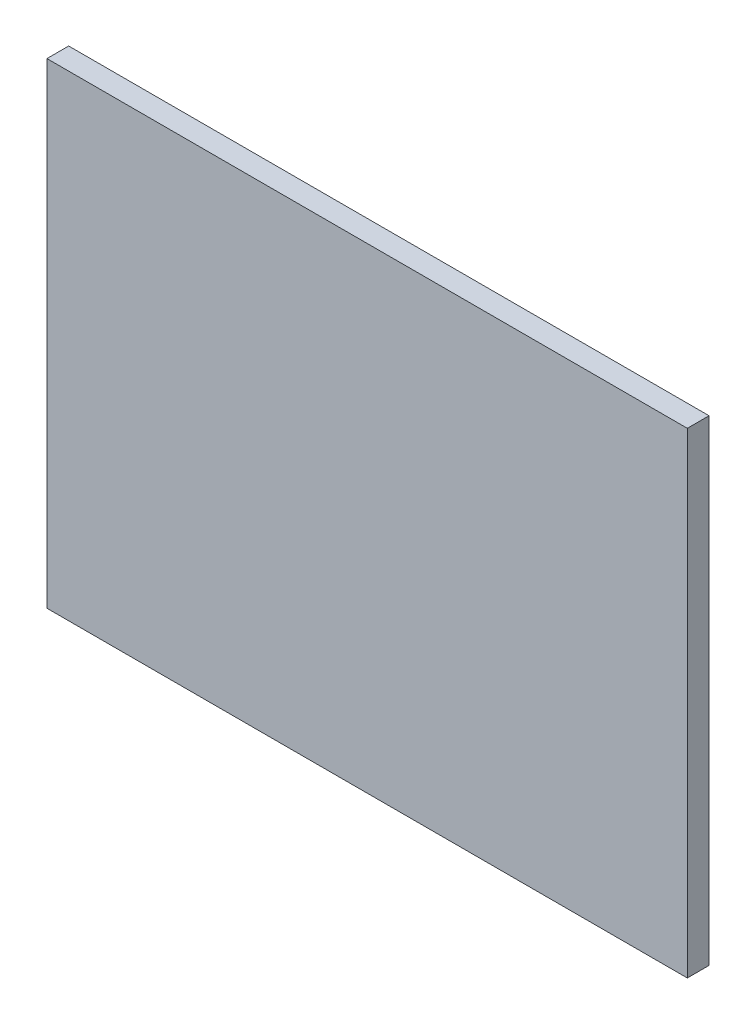
SolidWorks part; units mm, degrees
material "Balsa"
ref_plane "Front Plane" through (0, 0, 0) normal (0, 0, 1) x (1, 0, 0)
ref_plane "Top Plane" through (0, 0, 0) normal (0, 1, 0) x (1, 0, 0)
ref_plane "Right Plane" through (0, 0, 0) normal (1, 0, 0) x (0, 0, -1)
sketch "Sketch1" plane through (0, 0, 0) normal (0, 0, 1) x (1, 0, 0)
  line L1 (-265, 197) -> (265, 197)
  line L2 (-265, 197) -> (-265, -197)
  line L3 (-265, -197) -> (265, -197)
  line L4 (265, 197) -> (265, -197)
  line L5 (-265, 197) -> (265, -197) construction
  line L6 (-265, -197) -> (265, 197) construction
  point P0 (0, 0)
  dimension "D1" = 530
  dimension "D2" = 394
extrude "Boss-Extrude1" add sketch "Sketch1" along normal blind 18
